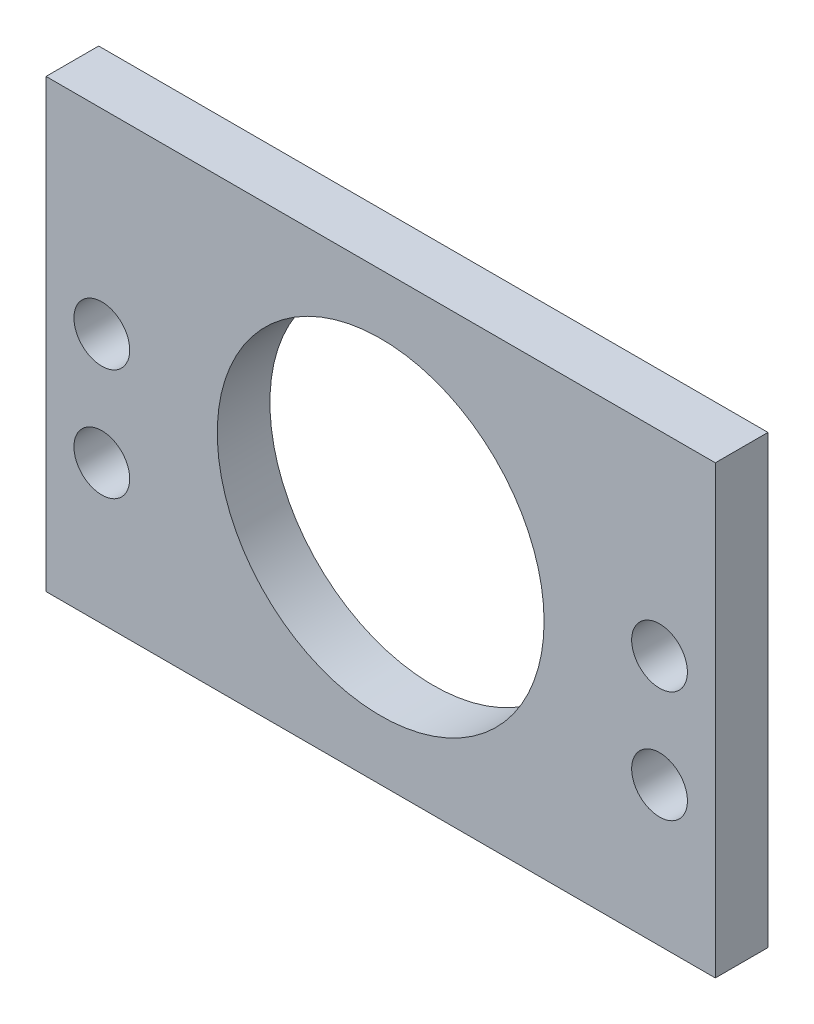
SolidWorks part; units mm, degrees
ref_plane "Front Plane" through (0, 0, 0) normal (0, 0, 1) x (1, 0, 0)
ref_plane "Top Plane" through (0, 0, 0) normal (0, 1, 0) x (1, 0, 0)
ref_plane "Right Plane" through (0, 0, 0) normal (1, 0, 0) x (0, 0, -1)
sketch "Sketch1" plane through (0, 0, 0) normal (0, 0, 1) x (1, 0, 0)
  line L0 (38.1, 50.8) -> (38.1, 25.4) construction
  line L1 (0, 0) -> (76.2, 0)
  line L2 (0, 0) -> (0, 50.8)
  line L3 (0, 50.8) -> (76.2, 50.8)
  line L4 (76.2, 0) -> (76.2, 50.8)
  circle A0 centre (38.1, 25.4) radius 18.6055
  circle A1 centre (6.35, 28.575) radius 3.175
  circle A2 centre (6.35, 15.875) radius 3.175
  circle A3 centre (69.85, 28.575) radius 3.175
  circle A4 centre (69.85, 15.875) radius 3.175
  dimension "D3" = 37.211
  dimension "D5" = 15.875
  dimension "D7" = 6.35
  dimension "D8" = 6.35
  dimension "D9" = 6.35
  dimension "D1" = 76.2
  dimension "D2" = 50.8
  dimension "D4" = 25.4
  dimension "D6" = 12.7
extrude "Boss-Extrude1" add sketch "Sketch1" along normal blind 5.9944
